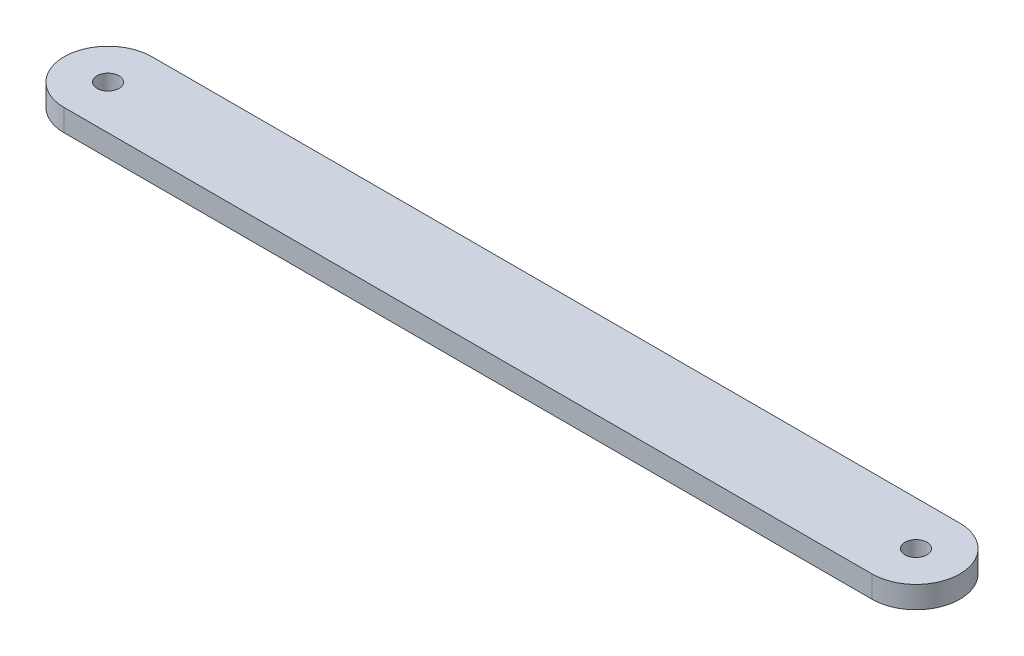
SolidWorks part; units mm, degrees
ref_plane "Front Plane" through (0, 0, 0) normal (0, 0, 1) x (1, 0, 0)
ref_plane "Top Plane" through (0, 0, 0) normal (0, 1, 0) x (1, 0, 0)
ref_plane "Right Plane" through (0, 0, 0) normal (1, 0, 0) x (0, 0, -1)
sketch "Sketch1" plane through (0, 0, 0) normal (0, 1, 0) x (1, 0, 0)
  line L0 (0, 0) -> (233.53, 0) construction
  line L1 (0, 12.7) -> (233.53, 12.7)
  line L2 (0, -12.7) -> (233.53, -12.7)
  circle A0 centre (0, 0) radius 3.175
  circle A1 centre (233.53, 0) radius 3.175
  arc A2 (0, 12.7) -> (0, -12.7) centre (0, 0) ccw
  arc A3 (233.53, -12.7) -> (233.53, 12.7) centre (233.53, 0) ccw
  point P5 (116.765, 0)
  dimension "D1" = 6.35
  dimension "D2" = 6.35
  dimension "D3" = 233.53
  dimension "D4" = 25.4
extrude "Boss-Extrude1" add sketch "Sketch1" along normal blind 6.35
